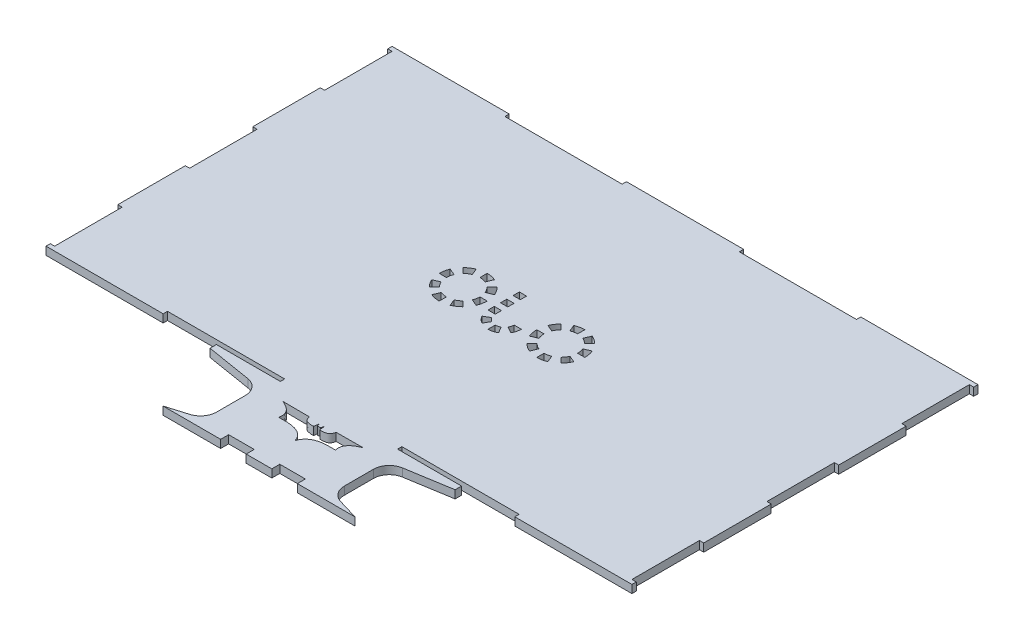
SolidWorks part; units mm, degrees
ref_plane "Front Plane" through (0, 0, 0) normal (0, 0, 1) x (1, 0, 0)
ref_plane "Top Plane" through (0, 0, 0) normal (0, 1, 0) x (1, 0, 0)
ref_plane "Right Plane" through (0, 0, 0) normal (1, 0, 0) x (0, 0, -1)
sketch "Sketch1" plane through (0, 0, 0) normal (0, 1, 0) x (1, 0, 0)
  line L0 (-183.2, 108.2) -> (-109.92, 108.2)
  line L1 (-109.92, 105.5) -> (-36.64, 105.5)
  line L4 (180.5, 105.5) -> (180.5, 63.3)
  line L5 (183.2, 108.2) -> (183.2, 105.5)
  line L8 (183.2, 63.3) -> (183.2, 21.1)
  line L9 (183.2, 108.2) -> (183.2, -108.2) construction
  line L10 (180.5, -105.5) -> (183.2, -105.5)
  line L11 (180.5, 105.5) -> (183.2, 105.5)
  line L13 (180.5, 105.5) -> (180.5, -105.5) construction
  line L14 (180.5, 21.1) -> (180.5, -21.1)
  line L16 (180.5, -63.3) -> (180.5, -105.5)
  line L18 (-180.5, 105.5) -> (-180.5, -105.5) construction
  line L23 (-183.2, 108.2) -> (183.2, 108.2) construction
  line L24 (-36.64, 108.2) -> (36.64, 108.2)
  line L26 (109.92, 108.2) -> (183.2, 108.2)
  line L27 (-109.92, 108.2) -> (-109.92, 105.5)
  line L28 (-36.64, 108.2) -> (-36.64, 105.5)
  line L29 (36.64, 108.2) -> (36.64, 105.5)
  line L30 (109.92, 108.2) -> (109.92, 105.5)
  line L31 (-180.5, 105.5) -> (180.5, 105.5) construction
  line L32 (36.64, 105.5) -> (109.92, 105.5)
  line L33 (-183.2, -108.2) -> (183.2, -108.2) construction
  line L34 (-180.5, -105.5) -> (180.5, -105.5) construction
  line L35 (180.5, -21.1) -> (183.2, -21.1)
  line L36 (109.92, -108.2) -> (183.2, -108.2)
  line L37 (109.92, -108.2) -> (109.92, -105.5)
  line L38 (36.64, -105.5) -> (109.92, -105.5)
  line L39 (36.64, -108.2) -> (36.64, -105.5)
  line L41 (-36.64, -108.2) -> (-36.64, -105.5)
  line L42 (-109.92, -105.5) -> (-36.64, -105.5)
  line L43 (-109.92, -108.2) -> (-109.92, -105.5)
  line L44 (-183.2, -108.2) -> (-109.92, -108.2)
  line L45 (180.5, -63.3) -> (183.2, -63.3)
  line L46 (180.5, 21.1) -> (183.2, 21.1)
  line L47 (180.5, 63.3) -> (183.2, 63.3)
  line L48 (183.2, -21.1) -> (183.2, -63.3)
  line L49 (-183.2, 108.2) -> (-183.2, -108.2) construction
  line L50 (183.2, -105.5) -> (183.2, -108.2)
  line L51 (-40, -126.6956) -> (-40, -144.7597)
  line L52 (-183.2, -105.5) -> (-183.2, -108.2)
  line L53 (-180.5, -105.5) -> (-183.2, -105.5)
  line L54 (-180.5, -63.3) -> (-180.5, -105.5)
  line L55 (-180.5, -63.3) -> (-183.2, -63.3)
  line L56 (-183.2, -21.1) -> (-183.2, -63.3)
  line L57 (-180.5, -21.1) -> (-183.2, -21.1)
  line L58 (-180.5, 21.1) -> (-180.5, -21.1)
  line L59 (-180.5, 21.1) -> (-183.2, 21.1)
  line L60 (-183.2, 63.3) -> (-183.2, 21.1)
  line L61 (-180.5, 63.3) -> (-183.2, 63.3)
  line L62 (-180.5, 105.5) -> (-180.5, 63.3)
  line L63 (-183.2, 108.2) -> (-183.2, 105.5)
  line L64 (-180.5, 105.5) -> (-183.2, 105.5)
  line L67 (40, -126.6956) -> (40, -144.7597)
  line L70 (-40, -158.2) -> (-24, -158.2)
  line L71 (24, -153.2) -> (8, -153.2)
  line L75 (-8, -158.2) -> (8, -158.2)
  line L77 (24, -158.2) -> (40, -158.2)
  line L78 (-24, -158.2) -> (-24, -153.2)
  line L79 (-8, -158.2) -> (-8, -153.2)
  line L80 (8, -158.2) -> (8, -153.2)
  line L81 (24, -158.2) -> (24, -153.2)
  line L82 (-8, -153.2) -> (-24, -153.2)
  line L83 (-36.64, -108.2) -> (-76.64, -108.2)
  line L84 (36.64, -108.2) -> (76.64, -108.2)
  line L85 (-76.64, -108.2) -> (-76.64, -112.2)
  line L86 (-76.64, -112.2) -> (-48.384, -116.8271)
  line L87 (76.64, -108.2) -> (76.64, -112.2)
  line L88 (76.64, -112.2) -> (48.384, -116.8271)
  line L89 (-40, -158.2) -> (-60, -158.2)
  line L90 (40, -158.2) -> (60, -158.2)
  line L92 (-47.1265, -154.338) -> (-60, -158.2)
  line L94 (47.1265, -154.338) -> (60, -158.2)
  line L95 (0.9301, -120.7166) -> (0, -120.6808)
  line L96 (-10.416, 3.2488) -> (-10.416, 7.1658)
  line L147 (-10.416, 11.0829) -> (-10.416, 15)
  line L148 (-9.0207, -9.7927) -> (-5.1196, -7.5404)
  line L149 (-5.2087, -13.6047) -> (-2.9564, -9.7036)
  line L150 (-0.0014, -10.4954) -> (-0.0014, -15)
  line L151 (5.2059, -13.6047) -> (2.9536, -9.7036)
  line L152 (5.1168, -7.5404) -> (9.0179, -9.7927)
  line L153 (-5.9114, -4.5854) -> (-10.416, -4.5854)
  line L154 (-5.9083, -0.6683) -> (-10.416, -0.6683)
  line L155 (-5.9051, 3.2488) -> (-10.416, 3.2488)
  line L156 (-5.9019, 7.1658) -> (-10.416, 7.1658)
  line L157 (-5.8988, 11.0829) -> (-10.416, 11.0829)
  line L158 (-5.8988, 11.0829) -> (-5.8956, 15)
  line L159 (-5.9051, 3.2488) -> (-5.9019, 7.1658)
  line L160 (-10.416, -4.5854) -> (-10.416, -0.6683)
  line L161 (-5.9114, -4.5854) -> (-5.9083, -0.6683)
  line L162 (-10.416, 15) -> (-5.8956, 15)
  line L163 (10.4131, -4.5854) -> (5.9086, -4.5854)
  line L164 (-24.7875, -13.8582) -> (-26.5096, -9.7007)
  line L165 (-19.9211, -10.6066) -> (-23.1031, -7.4246)
  line L166 (-15.5278, 0) -> (-20.0278, 0)
  line L167 (-16.6696, -5.7403) -> (-20.827, -4.0182)
  line L168 (-19.9211, 10.6066) -> (-23.1031, 7.4246)
  line L169 (-16.6696, 5.7403) -> (-20.827, 4.0182)
  line L170 (-30.5278, 15) -> (-30.5278, 10.5)
  line L171 (-24.7875, 13.8582) -> (-26.5096, 9.7007)
  line L172 (-37.9524, 7.4246) -> (-41.1344, 10.6066)
  line L173 (-34.5459, 9.7007) -> (-36.268, 13.8582)
  line L174 (-41.0278, 0) -> (-45.5278, 0)
  line L175 (-40.2285, 4.0182) -> (-44.3859, 5.7403)
  line L176 (-37.9524, -7.4246) -> (-41.1344, -10.6066)
  line L177 (-40.2285, -4.0182) -> (-44.3859, -5.7403)
  line L178 (-30.5278, -10.5) -> (-30.5278, -15)
  line L179 (-34.5459, -9.7007) -> (-36.268, -13.8582)
  line L180 (24.7875, -13.8582) -> (26.5096, -9.7007)
  line L181 (30.5278, -10.5) -> (30.5278, -15)
  line L182 (34.5459, -9.7007) -> (36.268, -13.8582)
  line L183 (37.9524, -7.4246) -> (41.1344, -10.6066)
  line L184 (40.2285, -4.0182) -> (44.3859, -5.7403)
  line L185 (41.0278, 0) -> (45.5278, 0)
  line L186 (40.2285, 4.0182) -> (44.3859, 5.7403)
  line L187 (37.9524, 7.4246) -> (41.1344, 10.6066)
  line L188 (34.5459, 9.7007) -> (36.268, 13.8582)
  line L189 (30.5278, 15) -> (30.5278, 10.5)
  line L190 (24.7875, 13.8582) -> (26.5096, 9.7007)
  line L191 (19.9211, 10.6066) -> (23.1031, 7.4246)
  line L192 (16.6696, 5.7403) -> (20.827, 4.0182)
  line L193 (15.5278, 0) -> (20.0278, 0)
  line L194 (16.6696, -5.7403) -> (20.827, -4.0182)
  line L195 (19.9211, -10.6066) -> (23.1031, -7.4246)
  line L196 (1.4468, -118.9339) -> (0.9301, -120.7166)
  line L197 (25.0098, -118.2105) -> (8.3452, -118.288)
  line L198 (1.5053, -118.7321) -> (1.5244, -118.908)
  line L199 (1.5053, -118.7321) -> (1.4468, -118.9339)
  line L200 (-1.5053, -118.7321) -> (-1.4468, -118.9339)
  line L201 (-1.5053, -118.7321) -> (-1.5244, -118.908)
  line L202 (-25.0098, -118.2105) -> (-8.3452, -118.288)
  line L203 (-1.4468, -118.9339) -> (-0.9301, -120.7166)
  line L204 (-0.9301, -120.7166) -> (0, -120.6808)
  arc A0 (-48.384, -116.8271) -> (-40, -126.6956) centre (-50, -126.6956) cw
  arc A1 (40, -126.6956) -> (48.384, -116.8271) centre (50, -126.6956) cw
  arc A2 (-47.1265, -154.338) -> (-40, -144.7597) centre (-50, -144.7597) ccw
  arc A3 (40, -144.7597) -> (47.1265, -154.338) centre (50, -144.7597) ccw
  arc A42 (2.9536, -9.7036) -> (-0.0014, -10.4954) centre (-0.0014, -4.5854) cw
  arc A43 (-2.9564, -9.7036) -> (-5.1196, -7.5404) centre (-0.0014, -4.5854) cw
  arc A44 (-5.2087, -13.6047) -> (-9.0207, -9.7927) centre (-0.0014, -4.5854) cw
  arc A45 (5.2059, -13.6047) -> (-0.0014, -15) centre (-0.0014, -4.5854) cw
  arc A46 (5.9086, -4.5854) -> (5.1168, -7.5404) centre (-0.0014, -4.5854) cw
  arc A47 (10.4131, -4.5854) -> (9.0179, -9.7927) centre (-0.0014, -4.5854) cw
  arc A48 (-26.5096, -9.7007) -> (-23.1031, -7.4246) centre (-30.5278, 0) ccw
  arc A49 (-24.7875, -13.8582) -> (-19.9211, -10.6066) centre (-30.5278, 0) ccw
  arc A50 (-20.827, -4.0182) -> (-20.0278, 0) centre (-30.5278, 0) ccw
  arc A51 (-16.6696, -5.7403) -> (-15.5278, 0) centre (-30.5278, 0) ccw
  arc A52 (-20.827, 4.0182) -> (-23.1031, 7.4246) centre (-30.5278, 0) ccw
  arc A53 (-16.6696, 5.7403) -> (-19.9211, 10.6066) centre (-30.5278, 0) ccw
  arc A54 (-26.5096, 9.7007) -> (-30.5278, 10.5) centre (-30.5278, 0) ccw
  arc A55 (-24.7875, 13.8582) -> (-30.5278, 15) centre (-30.5278, 0) ccw
  arc A56 (-36.268, 13.8582) -> (-41.1344, 10.6066) centre (-30.5278, 0) ccw
  arc A57 (-34.5459, 9.7007) -> (-37.9524, 7.4246) centre (-30.5278, 0) ccw
  arc A58 (-44.3859, 5.7403) -> (-45.5278, 0) centre (-30.5278, 0) ccw
  arc A59 (-40.2285, 4.0182) -> (-41.0278, 0) centre (-30.5278, 0) ccw
  arc A60 (-44.3859, -5.7403) -> (-41.1344, -10.6066) centre (-30.5278, 0) ccw
  arc A61 (-40.2285, -4.0182) -> (-37.9524, -7.4246) centre (-30.5278, 0) ccw
  arc A62 (-36.268, -13.8582) -> (-30.5278, -15) centre (-30.5278, 0) ccw
  arc A63 (-34.5459, -9.7007) -> (-30.5278, -10.5) centre (-30.5278, 0) ccw
  arc A64 (40.2285, 4.0182) -> (41.0278, 0) centre (30.5278, 0) cw
  arc A65 (40.2285, -4.0182) -> (37.9524, -7.4246) centre (30.5278, 0) cw
  arc A66 (34.5459, -9.7007) -> (30.5278, -10.5) centre (30.5278, 0) cw
  arc A67 (26.5096, -9.7007) -> (23.1031, -7.4246) centre (30.5278, 0) cw
  arc A68 (20.827, -4.0182) -> (20.0278, 0) centre (30.5278, 0) cw
  arc A69 (20.827, 4.0182) -> (23.1031, 7.4246) centre (30.5278, 0) cw
  arc A70 (26.5096, 9.7007) -> (30.5278, 10.5) centre (30.5278, 0) cw
  arc A71 (16.6696, -5.7403) -> (15.5278, 0) centre (30.5278, 0) cw
  arc A72 (24.7875, -13.8582) -> (19.9211, -10.6066) centre (30.5278, 0) cw
  arc A73 (36.268, -13.8582) -> (30.5278, -15) centre (30.5278, 0) cw
  arc A74 (44.3859, -5.7403) -> (41.1344, -10.6066) centre (30.5278, 0) cw
  arc A75 (44.3859, 5.7403) -> (45.5278, 0) centre (30.5278, 0) cw
  arc A76 (36.268, 13.8582) -> (41.1344, 10.6066) centre (30.5278, 0) cw
  arc A77 (24.7875, 13.8582) -> (30.5278, 15) centre (30.5278, 0) cw
  arc A78 (34.5459, 9.7007) -> (37.9524, 7.4246) centre (30.5278, 0) cw
  arc A79 (16.6696, 5.7403) -> (19.9211, 10.6066) centre (30.5278, 0) cw
  spline S0 degree 3 poles (0, -135.7277) (-0.2584, -135.0818) (-0.4466, -134.4031) (-0.7751, -133.7899) (-1.0966, -133.1898) (-1.4897, -132.6232) (-1.9377, -132.1105) (-2.391, -131.5919) (-2.9056, -131.1213) (-3.4621, -130.7154) (-4.0576, -130.281) (-4.6993, -129.9012) (-5.374, -129.6044) (-6.2141, -129.2348) (-7.0911, -128.9401) (-7.9835, -128.7259) (-9.0354, -128.4735) (-10.1097, -128.3041) (-11.1872, -128.2092) (-12.586, -128.0861) (-13.9951, -128.0606) (-15.3986, -128.1059) (-16.1735, -128.1309) (-16.9488, -128.1403) (-17.7239, -128.1575) knots 0 0 0 0 1 1 1 2 2 2 3 3 3 4 4 4 5 5 5 6 6 6 7 7 7 8 8 8 8
  spline S1 degree 3 poles (-17.7239, -128.1575) (-17.6464, -127.503) (-17.4868, -126.853) (-17.4914, -126.194) (-17.4955, -125.602) (-17.5727, -125.0019) (-17.7497, -124.4371) (-17.9387, -123.8343) (-18.2232, -123.2555) (-18.5765, -122.7319) (-18.9621, -122.1603) (-19.4328, -121.6422) (-19.9459, -121.1817) (-20.533, -120.6546) (-21.1783, -120.1875) (-21.8578, -119.7865) (-22.8694, -119.1894) (-23.9755, -118.7674) (-25.0098, -118.2105) knots 0 0 0 0 1 1 1 2 2 2 3 3 3 4 4 4 5 5 5 6 6 6 6
  spline S2 degree 3 poles (2.0928, -122.1118) (2.0066, -121.9998) (1.8591, -121.915) (1.8344, -121.7759) (1.6664, -120.8292) (1.6277, -119.864) (1.5244, -118.908) knots 0 0 0 0 1 1 1 2 2 2 2
  spline S3 degree 3 poles (8.3452, -118.288) (8.173, -118.8564) (8.0758, -119.4532) (7.8285, -119.9932) (7.6484, -120.3864) (7.396, -120.758) (7.0792, -121.0525) (6.7709, -121.3391) (6.397, -121.5764) (5.9941, -121.6984) (5.1566, -121.952) (4.2806, -122.0712) (3.4104, -122.1635) (2.9733, -122.2098) (2.532, -122.129) (2.0928, -122.1118) knots 0 0 0 0 1 1 1 2 2 2 3 3 3 4 4 4 5 5 5 5
  spline S4 degree 3 poles (17.7239, -128.1575) (17.6464, -127.503) (17.4868, -126.853) (17.4914, -126.194) (17.4955, -125.602) (17.5727, -125.0019) (17.7497, -124.4371) (17.9387, -123.8343) (18.2232, -123.2555) (18.5765, -122.7319) (18.9621, -122.1603) (19.4328, -121.6422) (19.9459, -121.1817) (20.533, -120.6546) (21.1783, -120.1875) (21.8578, -119.7865) (22.8694, -119.1894) (23.9755, -118.7674) (25.0098, -118.2105) knots 0 0 0 0 1 1 1 2 2 2 3 3 3 4 4 4 5 5 5 6 6 6 6
  spline S5 degree 3 poles (-8.3452, -118.288) (-8.173, -118.8564) (-8.0758, -119.4532) (-7.8285, -119.9932) (-7.6484, -120.3864) (-7.396, -120.758) (-7.0792, -121.0525) (-6.7709, -121.3391) (-6.397, -121.5764) (-5.9941, -121.6984) (-5.1566, -121.952) (-4.2806, -122.0712) (-3.4104, -122.1635) (-2.9733, -122.2098) (-2.532, -122.129) (-2.0928, -122.1118) knots 0 0 0 0 1 1 1 2 2 2 3 3 3 4 4 4 5 5 5 5
  spline S6 degree 3 poles (-2.0928, -122.1118) (-2.0066, -121.9998) (-1.8591, -121.915) (-1.8344, -121.7759) (-1.6664, -120.8292) (-1.6277, -119.864) (-1.5244, -118.908) knots 0 0 0 0 1 1 1 2 2 2 2
  spline S7 degree 3 poles (0, -135.7277) (0.2584, -135.0818) (0.4466, -134.4031) (0.7751, -133.7899) (1.0966, -133.1898) (1.4897, -132.6232) (1.9377, -132.1105) (2.391, -131.5919) (2.9056, -131.1213) (3.4621, -130.7154) (4.0576, -130.281) (4.6993, -129.9012) (5.374, -129.6044) (6.2141, -129.2348) (7.0911, -128.9401) (7.9835, -128.7259) (9.0354, -128.4735) (10.1097, -128.3041) (11.1872, -128.2092) (12.586, -128.0861) (13.9951, -128.0606) (15.3986, -128.1059) (16.1735, -128.1309) (16.9488, -128.1403) (17.7239, -128.1575) knots 0 0 0 0 1 1 1 2 2 2 3 3 3 4 4 4 5 5 5 6 6 6 7 7 7 8 8 8 8
  point P0 (0, 0)
  point P58 (-40, -118.2)
  point P68 (40, -118.2)
  dimension "D2" = 10
  dimension "D3" = 10
  dimension "D6" = 10
  dimension "D7" = 10
  dimension "D1" = 2.7
  dimension "D4" = 40
  dimension "D5" = 40
extrude "Boss-Extrude1" add sketch "Sketch1" along normal blind 5
